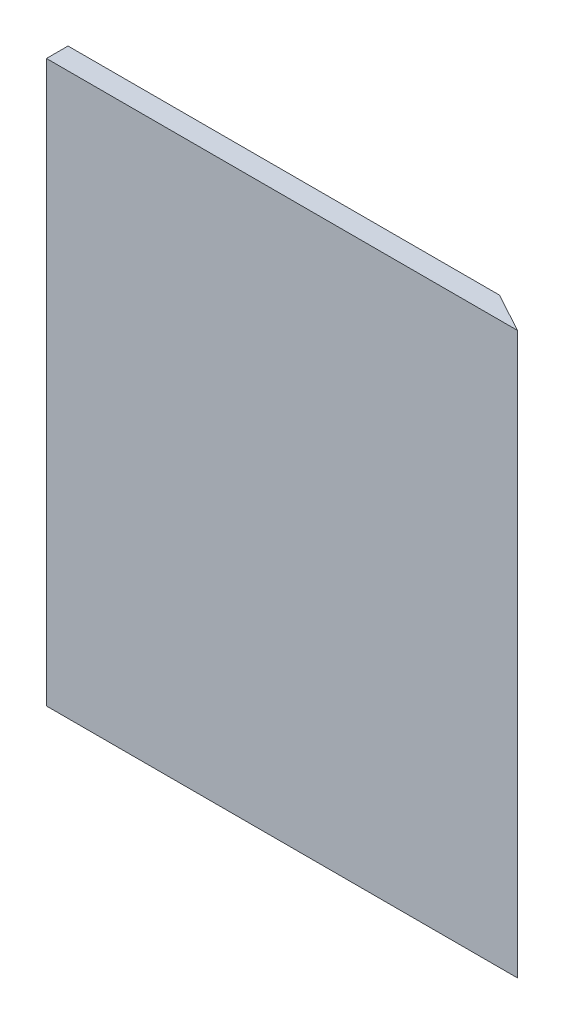
SolidWorks part; units mm, degrees
ref_plane "Front Plane" through (0, 0, 0) normal (0, 0, 1) x (1, 0, 0)
ref_plane "Top Plane" through (0, 0, 0) normal (0, 1, 0) x (1, 0, 0)
ref_plane "Right Plane" through (0, 0, 0) normal (1, 0, 0) x (0, 0, -1)
sketch "Sketch1" plane through (0, 0, 0) normal (0, 1, 0) x (1, 0, 0)
  line L0 (185.2874, 75.471) -> (208.6721, 62.771)
  line L2 (-68.7126, 75.471) -> (185.2874, 75.471)
  line L3 (-68.7126, 75.471) -> (-68.7126, 62.771)
  line L4 (-68.7126, 62.771) -> (185.2874, 62.771)
  line L7 (185.2874, 62.771) -> (208.6721, 62.771)
  dimension "D1" = 254
  dimension "D2" = 12.7
extrude "Boss-Extrude2" add sketch "Sketch1" along normal blind 330.2
